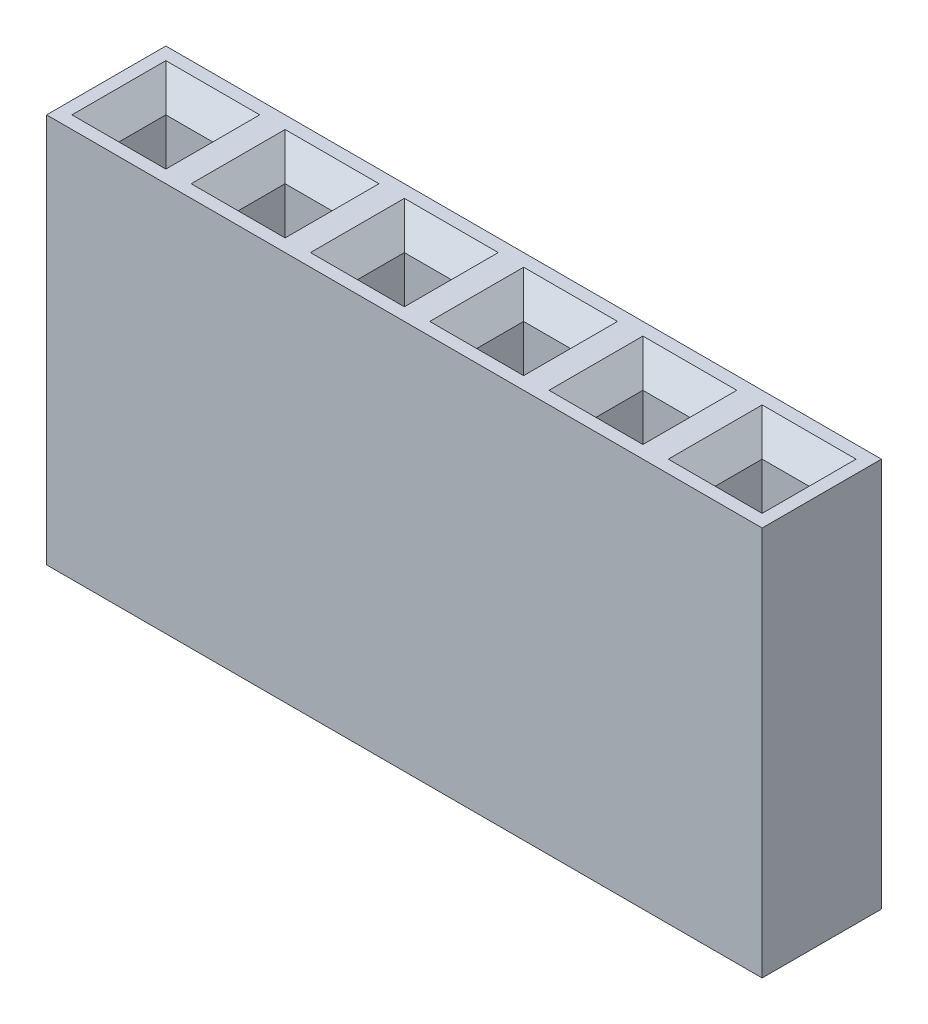
SolidWorks part; units mm, degrees
ref_plane "Front Plane" through (0, 0, 0) normal (0, 0, 1) x (1, 0, 0)
ref_plane "Top Plane" through (0, 0, 0) normal (0, 1, 0) x (1, 0, 0)
ref_plane "Right Plane" through (0, 0, 0) normal (1, 0, 0) x (0, 0, -1)
sketch "Sketch1" plane through (0, 0, 0) normal (0, 1, 0) x (1, 0, 0)
  line L0 (1.27, -1.27) -> (1.27, 1.27)
  line L1 (1.27, -1.27) -> (-1.27, -1.27)
  line L2 (1.27, 1.27) -> (-1.27, 1.27)
  line L3 (-1.27, -1.27) -> (-1.27, 1.27)
  line L4 (1.27, -1.27) -> (-1.27, 1.27) construction
  line L5 (1.27, 1.27) -> (-1.27, -1.27) construction
  point P1 (0, 0)
  dimension "D1" = 2.54
  dimension "D2" = 2.54
extrude "Boss-Extrude1" add sketch "Sketch1" along normal blind 8.3
sketch "Sketch2" plane through (0, 8.3, 0) normal (0, 1, 0) x (-1, 0, 0)
  line L0 (-0.5, 0.5) -> (-0.5, -0.5)
  line L1 (-0.5, 0.5) -> (0.5, 0.5)
  line L2 (-0.5, -0.5) -> (0.5, -0.5)
  line L3 (0.5, 0.5) -> (0.5, -0.5)
  line L4 (-0.5, 0.5) -> (0.5, -0.5) construction
  line L5 (-0.5, -0.5) -> (0.5, 0.5) construction
  point P1 (0, 0)
  dimension "D1" = 1
  dimension "D2" = 1
extrude "Cut-Extrude1" cut sketch "Sketch2" against normal blind 4
chamfer "Chamfer1" distance 0.5 angle 45 4 edges at (0, 8.3, 0.5) (0.5, 8.3, 0) (0, 8.3, -0.5) (-0.5, 8.3, 0)
pattern_linear "LPattern1" count 6 spacing 2.54 along (1, 0, 0) of "Boss-Extrude1", "Cut-Extrude1", "Chamfer1"
